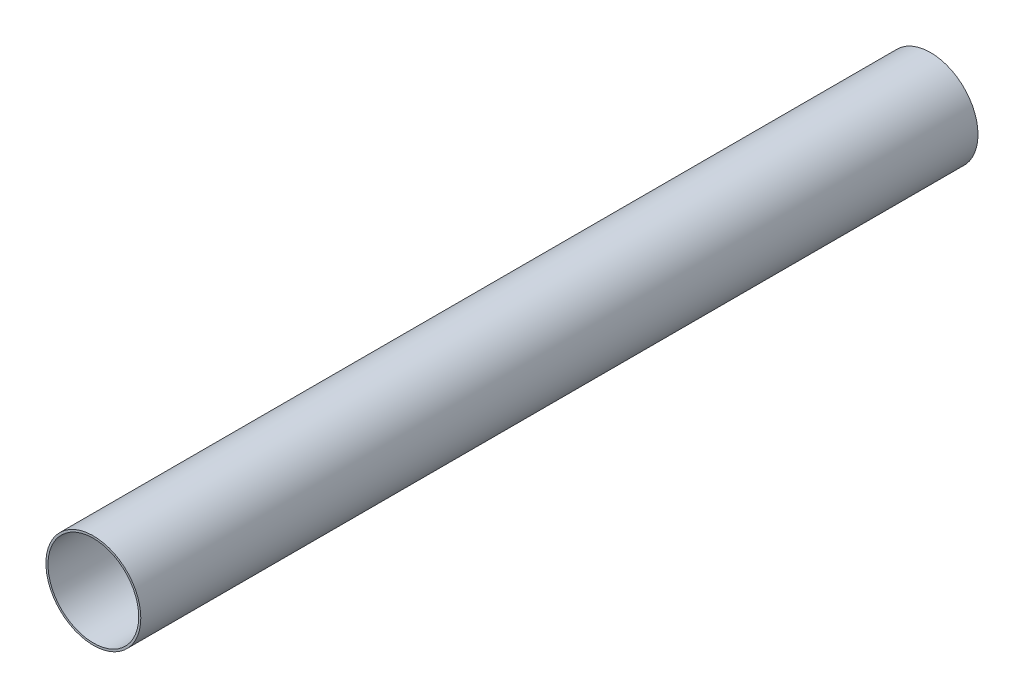
SolidWorks part; units mm, degrees
material "S-Glass Fiber"
ref_plane "Front Plane" through (0, 0, 0) normal (0, 0, 1) x (1, 0, 0)
ref_plane "Top Plane" through (0, 0, 0) normal (0, 1, 0) x (1, 0, 0)
ref_plane "Right Plane" through (0, 0, 0) normal (1, 0, 0) x (0, 0, -1)
sketch "Sketch1" plane through (0, 0, 0) normal (0, 0, 1) x (1, 0, 0)
  circle A0 centre (0, 0) radius 49.5554
  circle A1 centre (0, 0) radius 51.816
  dimension "D1" = 103.632
  dimension "D2" = 99.1108
extrude "Boss-Extrude1" add sketch "Sketch1" along normal blind 914.4
sketch "Sketch2" plane through (0, 0, 0) normal (0, 1, 0) x (1, 0, 0)
  line L0 (0, -914.4) -> (0, 0) construction
  line L1 (-51.816, -914.4) -> (51.816, -914.4) construction
